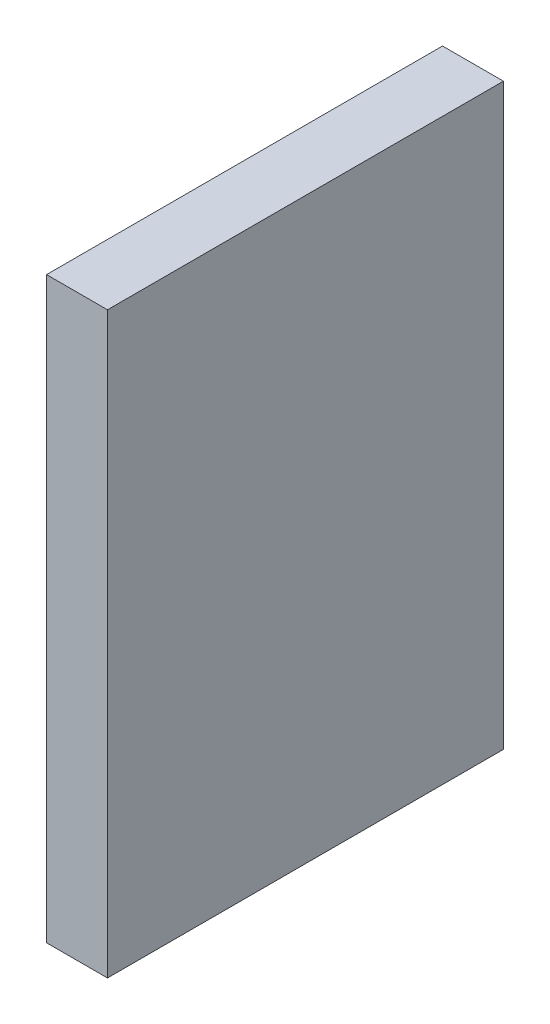
SolidWorks part; units mm, degrees
material "Rubber"
ref_plane "Alzado" through (0, 0, 0) normal (0, 0, 1) x (1, 0, 0)
ref_plane "Planta" through (0, 0, 0) normal (0, 1, 0) x (1, 0, 0)
ref_plane "Vista lateral" through (0, 0, 0) normal (1, 0, 0) x (0, 0, -1)
sketch "Sketch1" plane through (0, 0, 0) normal (0, 0, -1) x (1, 0, 0)
  line L0 (0, -9.5) -> (2, -9.5)
  line L1 (0, 0) -> (2, 0) construction
  line L2 (0, 0) -> (0, 9.5)
  line L3 (0, 9.5) -> (2, 9.5)
  line L4 (2, 0) -> (2, 9.5)
  line L23 (0, -9.5) -> (0, 0)
  line L24 (2, -9.5) -> (2, 0)
  dimension "D1" = 2
  dimension "D2" = 19
extrude "Boss-Extrude1" add sketch "Sketch1" along normal blind 13
